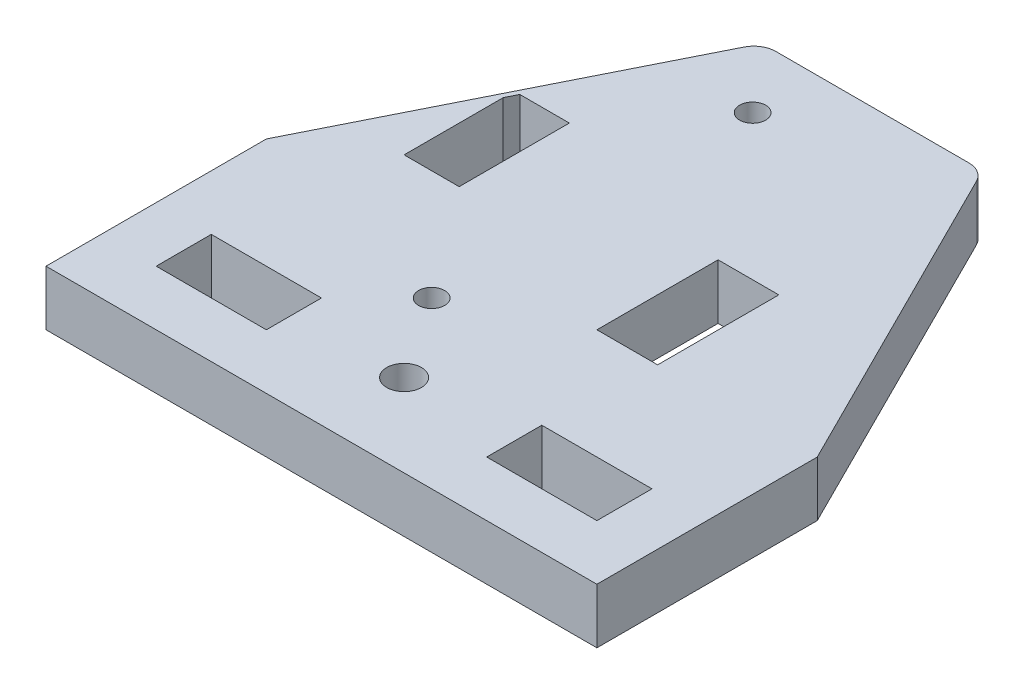
SolidWorks part; units mm, degrees
ref_plane "Front Plane" through (0, 0, 0) normal (0, 0, 1) x (1, 0, 0)
ref_plane "Top Plane" through (0, 0, 0) normal (0, 1, 0) x (1, 0, 0)
ref_plane "Right Plane" through (0, 0, 0) normal (1, 0, 0) x (0, 0, -1)
sketch "Sketch2" plane through (0, 0, 0) normal (0, 1, 0) x (1, 0, 0)
  line L0 (0, 25.4) -> (25.4, 76.2)
  line L1 (0, 0) -> (63.5, 0)
  line L2 (0, 0) -> (0, 25.4)
  line L3 (25.4, 76.2) -> (38.1, 76.2)
  line L4 (63.5, 0) -> (63.5, 25.4)
  line L5 (6.35, 6.35) -> (19.05, 6.35)
  line L6 (6.35, 6.35) -> (6.35, 12.7)
  line L7 (6.35, 12.7) -> (19.05, 12.7)
  line L8 (19.05, 6.35) -> (19.05, 12.7)
  line L9 (44.45, 6.35) -> (57.15, 6.35)
  line L10 (44.45, 6.35) -> (44.45, 12.7)
  line L11 (44.45, 12.7) -> (57.15, 12.7)
  line L12 (57.15, 6.35) -> (57.15, 12.7)
  line L13 (38.1, 39.37) -> (45.1, 39.37)
  line L14 (38.1, 39.37) -> (38.1, 25.4)
  line L15 (38.1, 25.4) -> (45.1, 25.4)
  line L16 (45.1, 39.37) -> (45.1, 25.4)
  line L17 (38.1, 39.37) -> (45.1, 25.4) construction
  line L18 (38.1, 25.4) -> (45.1, 39.37) construction
  line L19 (38.1, 76.2) -> (63.5, 25.4)
  circle A0 centre (31.75, 9.525) radius 2
  circle A1 centre (25.4, 19.05) radius 1.5
  circle A2 centre (25.4, 56.05) radius 1.5
  point P6 (41.6, 32.385)
  dimension "D4" = 6.35
  dimension "D7" = 4
  dimension "D12" = 9.525
  dimension "D17" = 3
  dimension "D18" = 3
  dimension "D19" = 6.35
  dimension "D1" = 63.5
  dimension "D3" = 12.7
  dimension "D5" = 6.35
  dimension "D6" = 12.7
  dimension "D8" = 12.7
  dimension "D9" = 12.7
  dimension "D10" = 6.35
  dimension "D11" = 6.35
  dimension "D13" = 6.35
  dimension "D14" = 13.97
  dimension "D15" = 7
  dimension "D16" = 37
  dimension "D20" = 12.7
  dimension "D21" = 6.35
  dimension "D22" = 6.35
  dimension "D23" = 6.35
  dimension "D26" = 50.8
  dimension "D27" = 50.8
extrude "Boss-Extrude1" add sketch "Sketch2" along normal blind 6.35
sketch "Sketch3" plane through (0, 6.35, 0) normal (0, 1, 0) x (1, 0, 0)
  line L0 (19.05, 12.7) -> (6.35, 12.7) construction
  line L1 (10.16, 44.45) -> (15.875, 44.45)
  line L2 (9.525, 43.18) -> (9.525, 31.75)
  line L3 (9.525, 31.75) -> (15.875, 31.75)
  line L4 (15.875, 44.45) -> (15.875, 31.75)
  line L5 (9.8425, 43.815) -> (15.875, 31.75) construction
  line L6 (9.525, 31.75) -> (15.875, 44.45) construction
  line L7 (10.16, 44.45) -> (9.525, 43.18)
  circle A0 centre (25.4, 19.05) radius 1.5 construction
  point P0 (12.7, 38.1)
  dimension "D2" = 12.7
  dimension "D3" = 12.7
  dimension "D4" = 25.4
extrude "Cut-Extrude7" cut sketch "Sketch3" against normal blind 6.35
sketch "Sketch4" plane through (0, 6.35, 0) normal (0, 1, 0) x (1, 0, 0)
  line L0 (19.05, 63.5) -> (44.45, 63.5)
  line L1 (25.4, 76.2) -> (0, 25.4) construction
  line L2 (63.5, 25.4) -> (38.1, 76.2) construction
  line L3 (38.1, 76.2) -> (25.4, 76.2) construction
  dimension "D1" = 12.7
extrude "Cut-Extrude8" cut sketch "Sketch4" against normal blind 6.35 and the other way through all
sketch "Sketch5" plane through (0, 6.35, 0) normal (0, 1, 0) x (1, 0, 0)
  line L0 (14.5498, 54.4997) -> (18.348, 62.0959) construction
  line L1 (19.05, 63.5) -> (0, 25.4) construction
  line L2 (20.6198, 63.5) -> (42.8802, 63.5) construction
  line L3 (45.152, 62.0959) -> (50.4774, 51.4451) construction
  line L4 (63.5, 25.4) -> (44.45, 63.5) construction
  arc A0 (45.152, 62.0959) -> (42.8802, 63.5) centre (42.8802, 60.96) ccw
  arc A1 (20.6198, 63.5) -> (18.348, 62.0959) centre (20.6198, 60.96) ccw
  point P12 (44.45, 63.5)
  point P15 (19.05, 63.5)
  dimension "D1" = 2.54
extrude "Cut-Extrude-Thin1" cut sketch "Sketch5" against normal blind 6.35 thin
